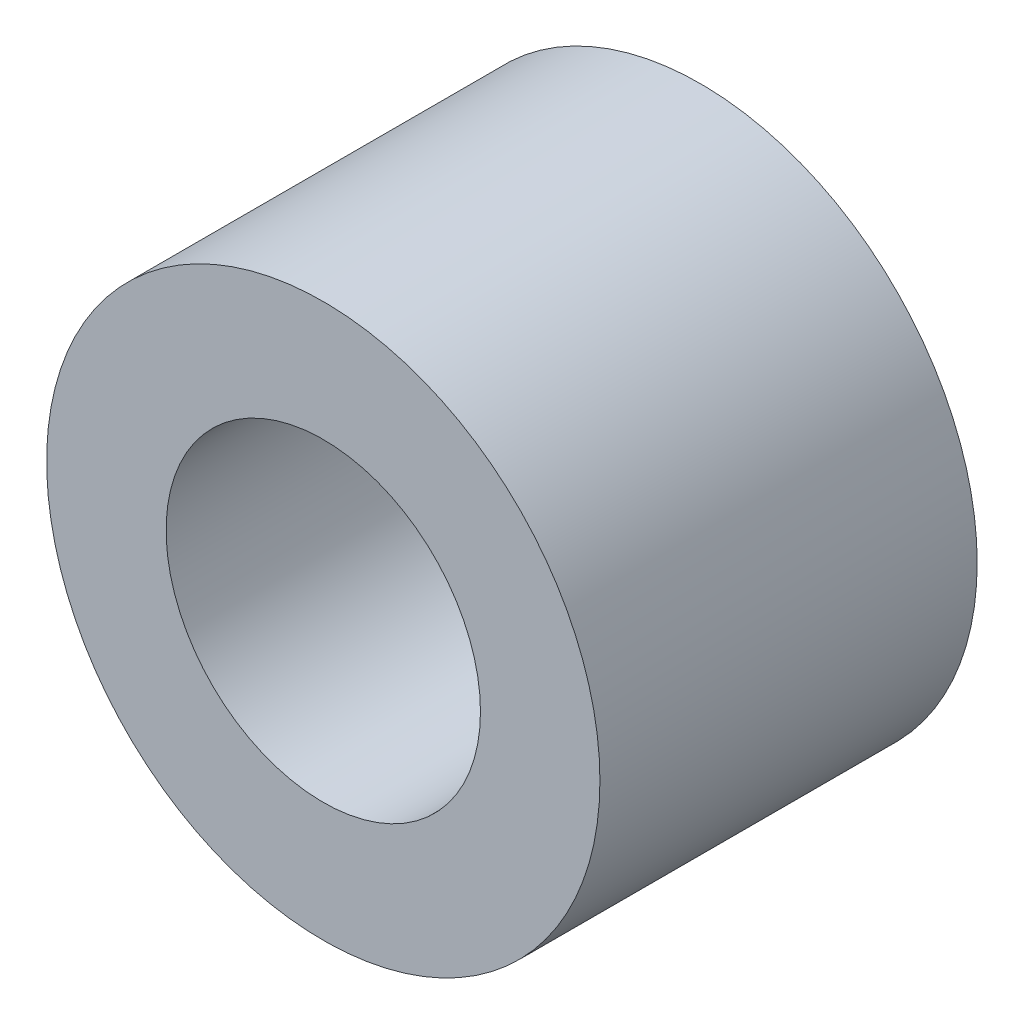
SolidWorks part; units mm, degrees
ref_plane "前视基准面" through (0, 0, 0) normal (0, 0, 1) x (1, 0, 0)
ref_plane "上视基准面" through (0, 0, 0) normal (0, 1, 0) x (1, 0, 0)
ref_plane "右视基准面" through (0, 0, 0) normal (1, 0, 0) x (0, 0, -1)
sketch "草图1" plane through (0, 0, 0) normal (0, 0, 1) x (1, 0, 0)
  circle A0 centre (0, 0) radius 1.25
  circle A1 centre (0, 0) radius 2.2
extrude "凸台-拉伸2" add sketch "草图1" along normal blind 3
